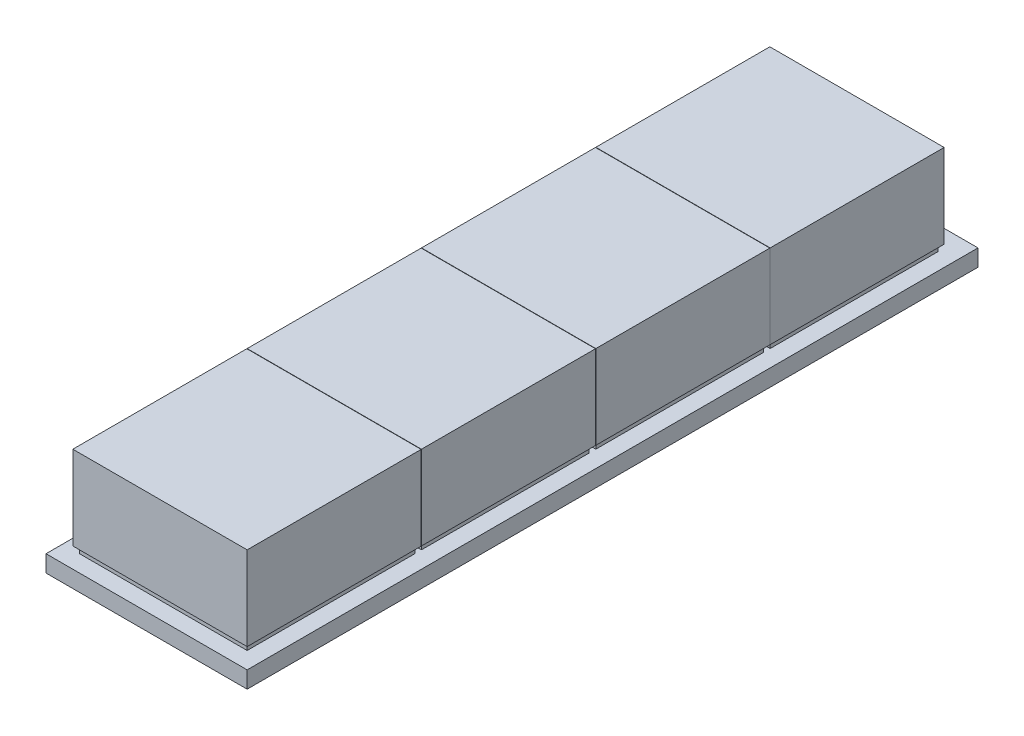
SolidWorks part; units mm, degrees
ref_plane "Front Plane" through (0, 0, 0) normal (0, 0, 1) x (1, 0, 0)
ref_plane "Top Plane" through (0, 0, 0) normal (0, 1, 0) x (1, 0, 0)
ref_plane "Right Plane" through (0, 0, 0) normal (1, 0, 0) x (0, 0, -1)
sketch "Sketch1" plane through (0, 0, 0) normal (0, 1, 0) x (1, 0, 0)
  line L1 (-30, -109) -> (30, -109)
  line L2 (-30, -109) -> (-30, 109)
  line L3 (-30, 109) -> (30, 109)
  line L4 (30, -109) -> (30, 109)
  line L5 (-30, -109) -> (30, 109) construction
  line L6 (-30, 109) -> (30, -109) construction
  point P0 (0, 0)
  dimension "D1" = 60
  dimension "D2" = 218
extrude "Boss-Extrude1" add sketch "Sketch1" along normal blind 5
sketch "Sketch2" plane through (0, 5, 0) normal (0, 1, 0) x (1, 0, 0)
  line L0 (0, 0) -> (0, -109) construction
  line L1 (-30, -109) -> (30, -109) construction
  line L3 (-25, -54) -> (25, -54)
  line L4 (-25, -54) -> (-25, -104)
  line L5 (-25, -104) -> (25, -104)
  line L6 (25, -54) -> (25, -104)
  line L7 (-25, -54) -> (25, -104) construction
  line L8 (-25, -104) -> (25, -54) construction
  point P5 (0, -79)
  dimension "D1" = 50
  dimension "D2" = 50
  dimension "D3" = 5
extrude "Boss-Extrude3" add sketch "Sketch2" along normal blind 2
pattern_linear "LPattern1" count 4 spacing 52 along (0, 0, -1) of "Boss-Extrude3"
sketch "Sketch3" plane through (0, 7, 0) normal (0, 1, 0) x (1, 0, 0)
  line L0 (0, 0) -> (0, -104) construction
  line L1 (-25, -104) -> (25, -104) construction
  line L3 (-26, -53.1) -> (26, -53.1)
  line L4 (-26, -53.1) -> (-26, -105)
  line L5 (-26, -105) -> (26, -105)
  line L6 (26, -53.1) -> (26, -105)
  line L7 (-26, -53.1) -> (26, -105) construction
  line L8 (-26, -105) -> (26, -53.1) construction
  line L9 (-30, -109) -> (30, -109) construction
  point P5 (0, -79.05)
  dimension "D1" = 52
  dimension "D2" = 51.9
  dimension "D3" = 4
extrude "Boss-Extrude8" add sketch "Sketch3" along normal blind 25
pattern_linear "LPattern5" count 4 spacing 52 along (0, 0, -1) of "Boss-Extrude8"
